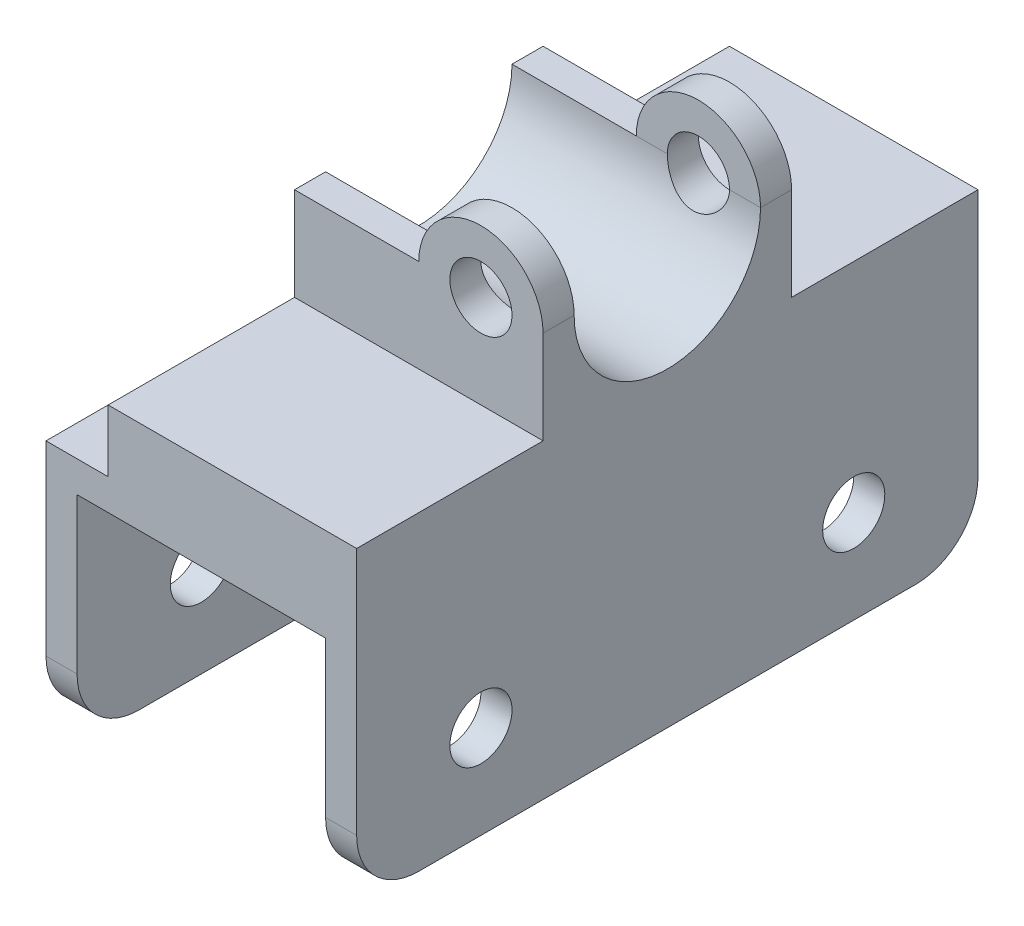
SolidWorks part; units mm, degrees
ref_plane "Front Plane" through (0, 0, 0) normal (0, 0, 1) x (1, 0, 0)
ref_plane "Top Plane" through (0, 0, 0) normal (0, 1, 0) x (1, 0, 0)
ref_plane "Right Plane" through (0, 0, 0) normal (1, 0, 0) x (0, 0, -1)
sketch "Sketch1" plane through (0, 0, 0) normal (0, 0, 1) x (1, 0, 0)
  line L0 (-34.0769, 0) -> (5, 0) construction
  line L1 (5, 0) -> (5, 65) construction
  line L2 (0, 0) -> (5, 0)
  line L3 (0, 0) -> (0, 65)
  line L4 (0, 75) -> (5, 75)
  line L5 (50, 0) -> (50, 65)
  line L6 (40, 75) -> (45, 75) construction
  line L11 (45, 75) -> (45, 0) construction
  line L12 (50, 45) -> (0, 45) construction
  line L13 (0, 45) -> (0, 65) construction
  line L14 (0, 65) -> (50, 65) construction
  line L15 (40, 65) -> (40, 75) construction
  line L16 (45, 0) -> (50, 0)
  line L18 (5, 0) -> (5, 45)
  line L19 (5, 45) -> (45, 45)
  line L20 (45, 0) -> (45, 45)
  line L21 (45, 0) -> (56.0769, 0) construction
  line L22 (0, 65) -> (30, 65)
  line L23 (40, 75) -> (45, 75)
  circle A1 centre (40, 65) radius 5
  arc A2 (50, 65) -> (30, 65) centre (40, 65) ccw
  dimension "D1" = 75
  dimension "D3" = 5
  dimension "D4" = 5
  dimension "D5" = 10
  dimension "D6" = 20
  dimension "D7" = 5
extrude "Boss-Extrude1" add sketch "Sketch1" along normal blind 100 contours L5 A2 L22 L3 L2 L18 L19 L20 L16 A1
sketch "Sketch2" plane through (50, 0, 0) normal (1, 0, 0) x (0, 0, -1)
  line L0 (-65, 65) -> (-65, 75)
  line L1 (-100, 65) -> (0, 65) construction
  line L4 (0, 75) -> (-100, 75) construction
  line L5 (-65, 75) -> (-35, 75)
  line L6 (-35, 75) -> (-35, 65)
  line L7 (-100, 75) -> (-100, 65) construction
  line L8 (-100, 75) -> (-70, 75)
  line L9 (-100, 75) -> (-100, 50)
  line L10 (-100, 50) -> (-70, 50)
  line L11 (-70, 75) -> (-70, 50)
  line L12 (0, 65) -> (0, 75) construction
  line L13 (0, 75) -> (-30, 75)
  line L14 (0, 75) -> (0, 50)
  line L15 (0, 50) -> (-30, 50)
  line L16 (-30, 75) -> (-30, 50)
  line L17 (-100, 15) -> (0, 15) construction
  line L18 (-100, 0) -> (-100, 65) construction
  line L19 (0, 0) -> (0, 65) construction
  line L20 (-100, 0) -> (0, 0) construction
  line L21 (-80, 15) -> (-80, 0) construction
  line L22 (-50, 15) -> (-50, 50) construction
  arc A2 (-65, 65) -> (-35, 65) centre (-50, 65) ccw
  circle A3 centre (-80, 15) radius 15 construction
  circle A4 centre (-80, 15) radius 5
  circle A5 centre (-20, 15) radius 5
  point P4 (-50, 65)
  dimension "D1" = 30
  dimension "D2" = 30
  dimension "D3" = 25
  dimension "D4" = 25
  dimension "D5" = 15
  dimension "D6" = 20
extrude "Cut-Extrude1" cut sketch "Sketch2" against normal blind 100
fillet "Fillet1" radius 10 4 edges at (2.5, 0, 0) (47.5, 0, 0) (2.5, 0, 100) (47.5, 0, 100)
sketch "Sketch4" plane through (0, 45, 0) normal (0, -1, 0) x (1, 0, 0)
  line L1 (5, 100) -> (45, 100)
  line L2 (5, 100) -> (5, 0)
  line L3 (5, 0) -> (45, 0)
  line L4 (45, 100) -> (45, 0)
extrude "Boss-Extrude2" add sketch "Sketch4" along normal blind 10
sketch "Sketch5" plane through (0, 0, 0) normal (0, 0, 1) x (1, 0, 0)
  line L1 (0, 65) -> (10, 65)
  line L2 (0, 65) -> (0, 45)
  line L3 (0, 45) -> (10, 45)
  line L4 (10, 65) -> (10, 45)
  dimension "D1" = 10
  dimension "D2" = 20
extrude "Cut-Extrude2" cut sketch "Sketch5" against normal through all and the other way through all
sketch "Sketch6" plane through (0, 0, 100) normal (0, 0, 1) x (1, 0, 0)
  line L1 (0, 45) -> (10, 45)
  line L2 (0, 45) -> (0, 40)
  line L3 (0, 40) -> (10, 40)
  line L4 (10, 45) -> (10, 40)
  dimension "D1" = 5
extrude "Cut-Extrude3" cut sketch "Sketch6" against normal through all both and the other way through all
